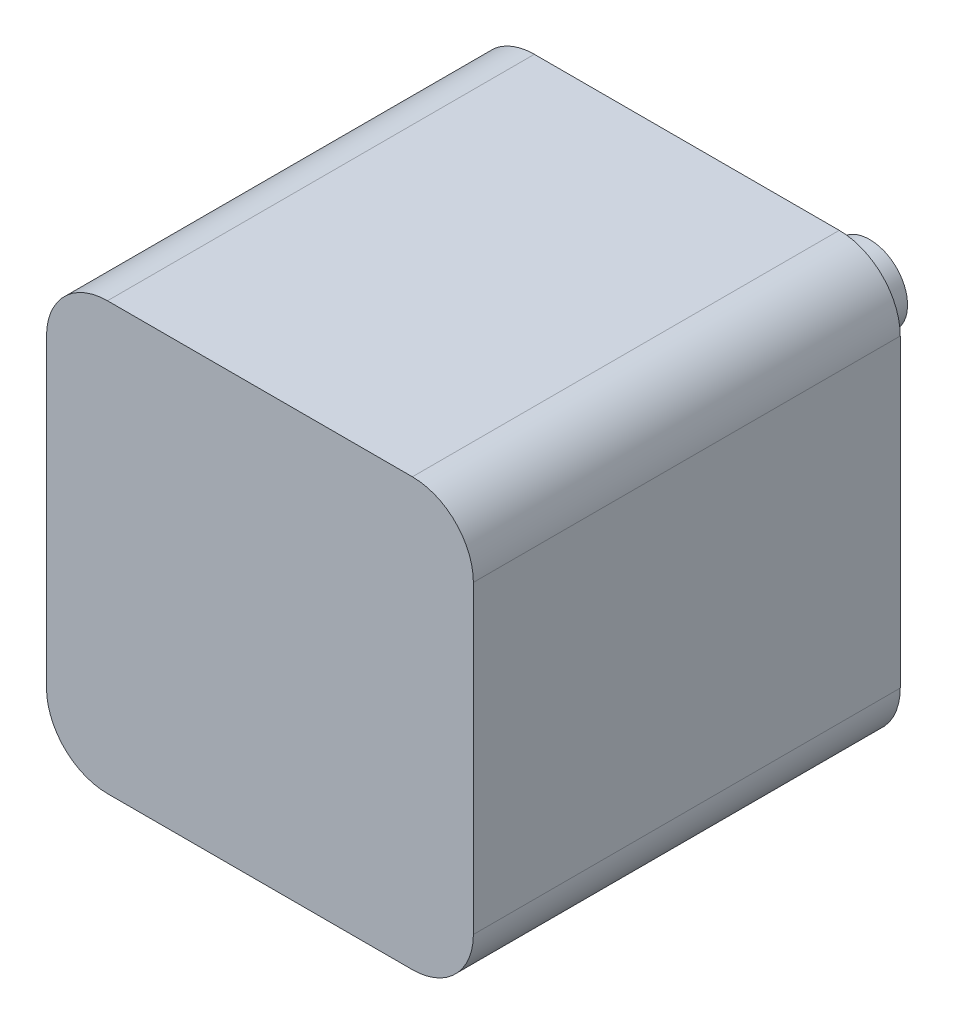
SolidWorks part; units mm, degrees
ref_plane "Front Plane" through (0, 0, 0) normal (0, 0, 1) x (1, 0, 0)
ref_plane "Top Plane" through (0, 0, 0) normal (0, 1, 0) x (1, 0, 0)
ref_plane "Right Plane" through (0, 0, 0) normal (1, 0, 0) x (0, 0, -1)
sketch "Sketch1" plane through (0, 0, 0) normal (0, 0, 1) x (1, 0, 0)
  line L1 (-8.89, -8.89) -> (8.89, -8.89)
  line L2 (-8.89, -8.89) -> (-8.89, 8.89)
  line L3 (-8.89, 8.89) -> (8.89, 8.89)
  line L4 (8.89, -8.89) -> (8.89, 8.89)
  line L5 (-8.89, -8.89) -> (8.89, 8.89) construction
  line L6 (-8.89, 8.89) -> (8.89, -8.89) construction
  point P0 (0, 0)
  dimension "D1" = 17.78
  dimension "D2" = 17.78
extrude "Boss-Extrude1" add sketch "Sketch1" along normal blind 17.78
fillet "Fillet1" radius 2.54 4 edges at (8.89, -8.89, 8.89) (-8.89, -8.89, 8.89) (-8.89, 8.89, 8.89) (8.89, 8.89, 8.89)
sketch "Sketch2" plane through (0, 0, 0) normal (0, 0, -1) x (-1, 0, 0)
  circle A0 centre (0, 0) radius 1.5744
extrude "Boss-Extrude2" add sketch "Sketch2" along normal blind 7.62
